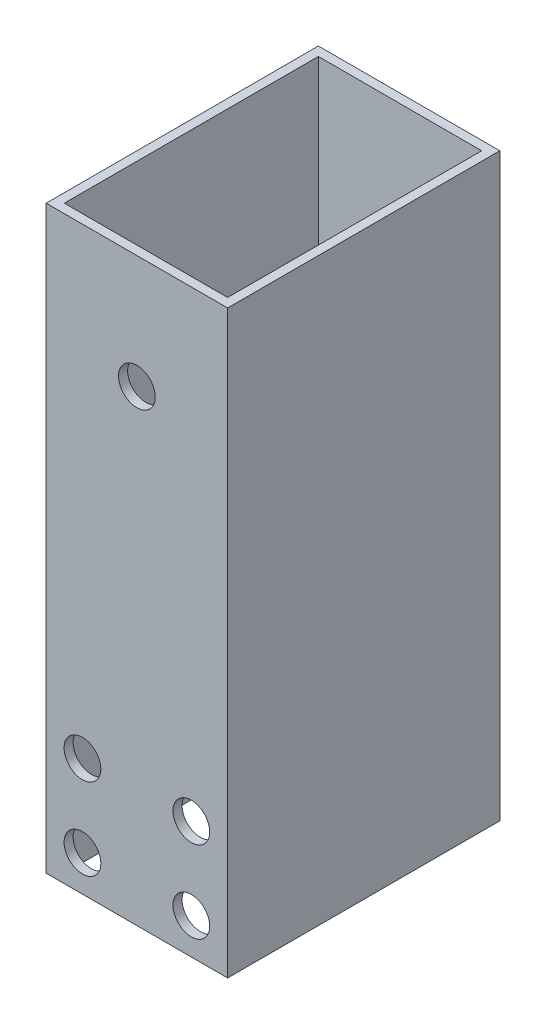
SolidWorks part; units mm, degrees
material "6063-T5"
ref_plane "前视基准面" through (0, 0, 0) normal (0, 0, 1) x (1, 0, 0)
ref_plane "上视基准面" through (0, 0, 0) normal (0, 1, 0) x (1, 0, 0)
ref_plane "右视基准面" through (0, 0, 0) normal (1, 0, 0) x (0, 0, -1)
other "Configuration Table"
sketch "草图2" plane through (0, 0, 0) normal (0, 1, 0) x (1, 0, 0)
  line L1 (-10, -15) -> (10, -15)
  line L2 (-10, -15) -> (-10, 15)
  line L3 (-10, 15) -> (10, 15)
  line L4 (10, -15) -> (10, 15)
  line L5 (-10, -15) -> (10, 15) construction
  line L6 (-10, 15) -> (10, -15) construction
  point P0 (0, 0)
  dimension "D1" = 30
  dimension "D2" = 20
extrude "凸台-拉伸1" add sketch "草图2" along normal mid plane 123
sketch "草图3" plane through (0, 0, 0) normal (0, 1, 0) x (1, 0, 0)
  line L8 (9, -14) -> (9, 14)
  line L9 (9, 14) -> (-9, 14)
  line L10 (-9, 14) -> (-9, -14)
  line L11 (-9, -14) -> (9, -14)
  line L12 (9, -14) -> (9, 14)
  line L13 (9, 14) -> (-9, 14)
  line L14 (-9, 14) -> (-9, -14)
  line L15 (-9, -14) -> (9, -14)
  dimension "D1" = 1
extrude "切除-拉伸1" cut sketch "草图3" against normal through all both and the other way through all
sketch "草图4" plane through (-10, 0, 0) normal (-1, 0, 0) x (0, 0, 1)
  line L0 (-15, 61.5) -> (15, 61.5) construction
  line L1 (15, 16.45) -> (-15, 16.45)
  line L2 (15, 16.45) -> (15, 61.5)
  line L3 (15, 61.5) -> (-15, 61.5)
  line L4 (-15, 16.45) -> (-15, 61.5)
  line L5 (15, 16.45) -> (-15, 61.5) construction
  line L6 (15, 61.5) -> (-15, 16.45) construction
  line L7 (-15, 61.5) -> (-15, -61.5) construction
  line L8 (15, 61.5) -> (15, -61.5) construction
  point P0 (0, 38.975)
  dimension "D1" = 45.05
extrude "切除-拉伸2" cut sketch "草图4" against normal through all
sketch "草图5" plane through (0, 0, 15) normal (0, 0, 1) x (1, 0, 0)
  line L0 (10, 16.45) -> (10, -61.5) construction
  line L1 (-10, 16.45) -> (-10, -61.5) construction
  line L2 (-10, -61.5) -> (10, -61.5) construction
  circle A0 centre (-6, -48.55) radius 2.025
  circle A1 centre (6, -48.55) radius 2.025
  dimension "D1" = 4.05
  dimension "D2" = 4.05
  dimension "D4" = 4
  dimension "D3" = 12
  dimension "D5" = 4
  dimension "D6" = 12.95
extrude "切除-拉伸3" cut sketch "草图5" against normal through all
sketch "草图6" plane through (0, 0, 15) normal (0, 0, 1) x (1, 0, 0)
  line L0 (-10, 16.45) -> (-10, -61.5) construction
  line L1 (10, 16.45) -> (-10, 16.45)
  line L2 (10, 16.45) -> (10, 2.45)
  line L3 (10, 2.45) -> (-10, 2.45)
  line L4 (-10, 16.45) -> (-10, 2.45)
  dimension "D1" = 14
extrude "切除-拉伸4" cut sketch "草图6" against normal through all both
sketch "草图7" plane through (0, 0, 15) normal (0, 0, 1) x (1, 0, 0)
  line L1 (-6, -48.55) -> (6, -48.55) construction
  line L2 (-6, -48.55) -> (-6, -57.55) construction
  line L3 (-6, -57.55) -> (6, -57.55) construction
  line L4 (6, -48.55) -> (6, -57.55) construction
  circle A0 centre (-6, -57.55) radius 2.025
  circle A1 centre (6, -57.55) radius 2.025
  circle A2 centre (6, -48.55) radius 2.025 construction
  dimension "D2" = 4.05
  dimension "D1" = 9
extrude "切除-拉伸5" cut sketch "草图7" against normal through all both
sketch "草图8" plane through (0, 0, 15) normal (0, 0, 1) x (1, 0, 0)
  line L0 (-10, 2.45) -> (-10, -61.5) construction
  line L1 (-10, 2.45) -> (10, 2.45) construction
  circle A5 centre (0, -10.05) radius 2.025
  dimension "D1" = 4.05
  dimension "D2" = 10
  dimension "D3" = 12.5
extrude "切除-拉伸6" cut sketch "草图8" against normal through all
